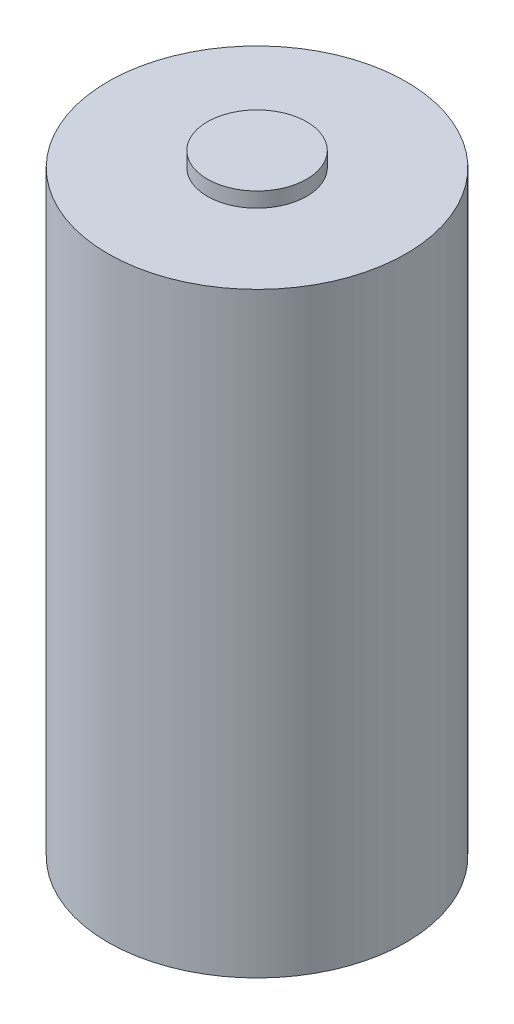
SolidWorks part; units mm, degrees
ref_plane "Front Plane" through (0, 0, 0) normal (0, 0, 1) x (1, 0, 0)
ref_plane "Top Plane" through (0, 0, 0) normal (0, 1, 0) x (1, 0, 0)
ref_plane "Right Plane" through (0, 0, 0) normal (1, 0, 0) x (0, 0, -1)
sketch "Sketch2" plane through (0, 0, 0) normal (0, 1, 0) x (1, 0, 0)
  circle A0 centre (0, 0) radius 3
  dimension "D1" = 6
extrude "Boss-Extrude1" add sketch "Sketch2" along normal blind 12
sketch "Sketch3" plane through (0, 12, 0) normal (0, 1, 0) x (1, 0, 0)
  circle A0 centre (0, 0) radius 1
  dimension "D1" = 2
extrude "Boss-Extrude2" add sketch "Sketch3" along normal blind 0.3
sketch "Sketch4" plane through (0, 0, 0) normal (0, -1, 0) x (-1, 0, 0)
  line L0 (0, -3) -> (0, 3) construction
  circle A0 centre (0, 0) radius 3 construction
  circle A1 centre (0, 2) radius 0.25
  circle A2 centre (0, -2) radius 0.25
  dimension "D1" = 0.5
  dimension "D2" = 0.5
  dimension "D3" = 1
  dimension "D4" = 1
extrude "Cut-Extrude1" cut sketch "Sketch4" against normal blind 0.1
